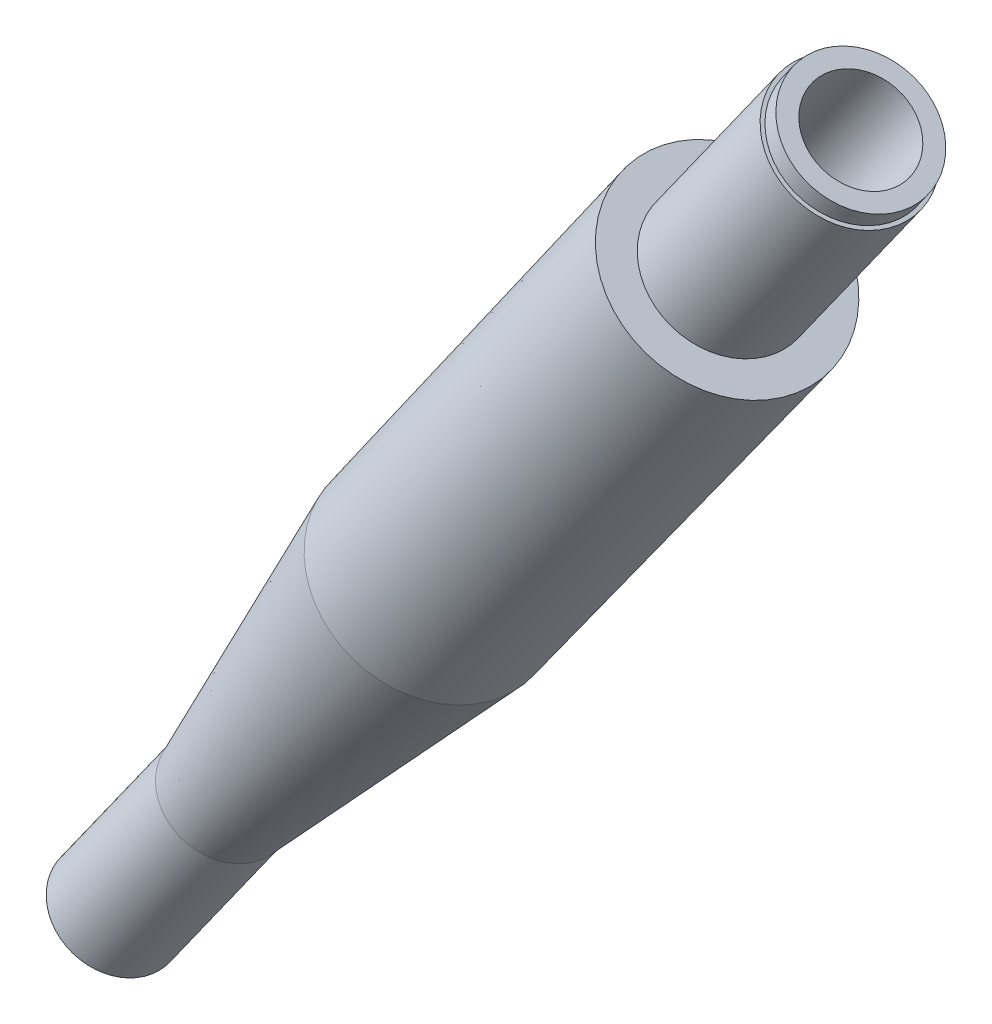
SolidWorks part; units mm, degrees
ref_plane "Front Plane" through (0, 0, 0) normal (0, 0, 1) x (1, 0, 0)
ref_plane "Top Plane" through (0, 0, 0) normal (0, 1, 0) x (1, 0, 0)
ref_plane "Right Plane" through (0, 0, 0) normal (1, 0, 0) x (0, 0, -1)
sketch "Sketch1" plane through (96.0319, 24.2599, -114.3264) normal (0, 0, -1) x (0.5798, 0.8148, 0)
  line L0 (-201.1453, 47.6197) -> (-136.9053, 47.6197)
  line L1 (-145.1453, 51.3147) -> (-145.1453, 53.0397)
  line L3 (-145.1453, 47.9809) -> (-145.1453, 50.1697)
  line L4 (-132.9053, 50.1697) -> (-132.9053, 51.3147)
  line L5 (-132.9053, 51.3147) -> (-145.1453, 51.3147)
  line L6 (-145.1453, 53.0397) -> (-172.1453, 52.8847)
  line L8 (-172.1453, 52.8847) -> (-191.1453, 50.4597)
  line L9 (-201.1453, 47.6197) -> (-201.1453, 50.4597)
  line L10 (-201.1453, 50.4597) -> (-191.1453, 50.4597)
  line L11 (-132.9053, 50.1697) -> (-145.1453, 50.1697)
  line L15 (-145.1453, 47.9809) -> (-136.9053, 47.9809)
  line L16 (-136.9053, 47.6197) -> (-136.9053, 47.9809)
  point P6 (-132.9053, 50.7422)
  dimension "D1" = 2.84
  dimension "D2" = 10
  dimension "D3" = 5.265
  dimension "D4" = 19
  dimension "D6" = 5.42
  dimension "D5" = 27
  dimension "D7" = 2.55
  dimension "D8" = 12.24
  dimension "D9" = 4
  dimension "D10" = 3.695
revolve "Revolve1" add sketch "Sketch1" angle 360 about L0
sketch "Sketch2" plane through (-33.3148, -46.8209, 0) normal (0.5798, 0.8148, 0) x (0.6639, -0.4724, -0.5798)
  circle A2 centre (157.3757, 28.3351) radius 3.495
  circle A3 centre (157.3757, 28.3351) radius 3.495
  dimension "D1" = 0.2
extrude "Cut-Extrude1" cut sketch "Sketch2" against normal blind 1 flip side to cut
